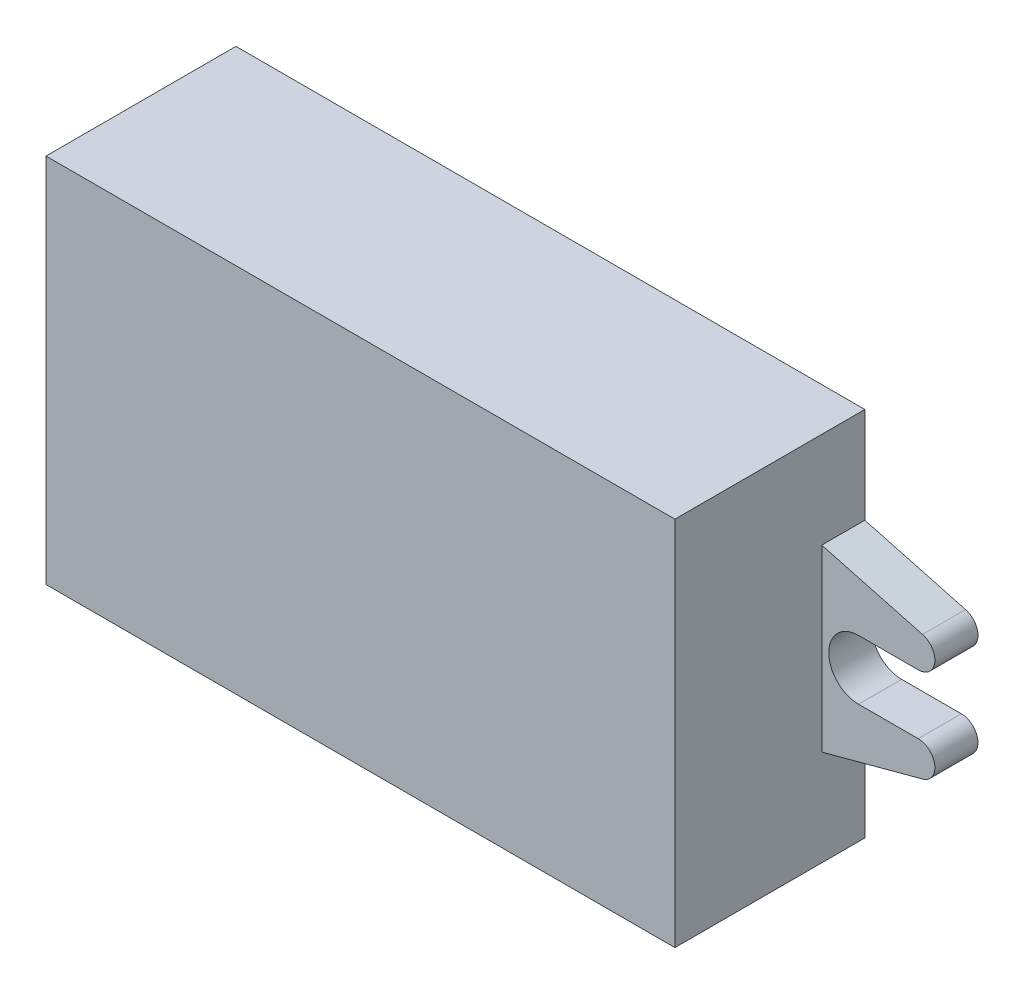
SolidWorks part; units mm, degrees
material "ABS"
ref_plane "Front Plane" through (0, 0, 0) normal (0, 0, 1) x (1, 0, 0)
ref_plane "Top Plane" through (0, 0, 0) normal (0, 1, 0) x (1, 0, 0)
ref_plane "Right Plane" through (0, 0, 0) normal (1, 0, 0) x (0, 0, -1)
sketch "Sketch1" plane through (0, 0, 0) normal (0, 0, 1) x (1, 0, 0)
  line L1 (-23.175, -13.675) -> (23.175, -13.675)
  line L2 (-23.175, -13.675) -> (-23.175, 13.675)
  line L3 (-23.175, 13.675) -> (23.175, 13.675)
  line L4 (23.175, -13.675) -> (23.175, 13.675)
  line L5 (-23.175, -13.675) -> (23.175, 13.675) construction
  line L6 (-23.175, 13.675) -> (23.175, -13.675) construction
  point P0 (0, 0)
  dimension "D1" = 46.35
  dimension "D2" = 27.35
extrude "Boss-Extrude1" add sketch "Sketch1" along normal blind 14
sketch "Sketch2" plane through (0, 0, 0) normal (0, 0, 1) x (1, 0, 0)
  line L0 (23.175, 6.6041) -> (30.6032, 4.6138)
  line L1 (23.175, -13.675) -> (23.175, 13.675) construction
  line L2 (30.2848, 2.1952) -> (25.8857, 2.1952)
  line L3 (0, 0) -> (23, 0) construction
  line L4 (30.2848, -2.1952) -> (25.8857, -2.1952)
  line L5 (23.175, -6.6041) -> (30.6032, -4.6138)
  line L6 (23.175, 6.6041) -> (23.175, -6.6041)
  line L7 (0, -19.0084) -> (0, 0) construction
  arc A0 (30.6032, 4.6138) -> (30.2848, 2.1952) centre (30.2848, 3.4254) cw
  arc A1 (30.6032, -4.6138) -> (30.2848, -2.1952) centre (30.2848, -3.4254) ccw
  arc A2 (25.8857, 2.1952) -> (25.8857, -2.1952) centre (25.8857, 0) ccw
  point P25 (23.6904, 0)
  dimension "D4" = 63.03
  dimension "D1" = 15
  dimension "D2" = 0.5154
  dimension "D3" = 4.3904
  dimension "D5" = 6.6041
extrude "Boss-Extrude2" add sketch "Sketch2" along normal blind 3.175
mirror "Mirror1" about plane through (0, 0, 0) normal (1, 0, 0) of "Boss-Extrude2"
